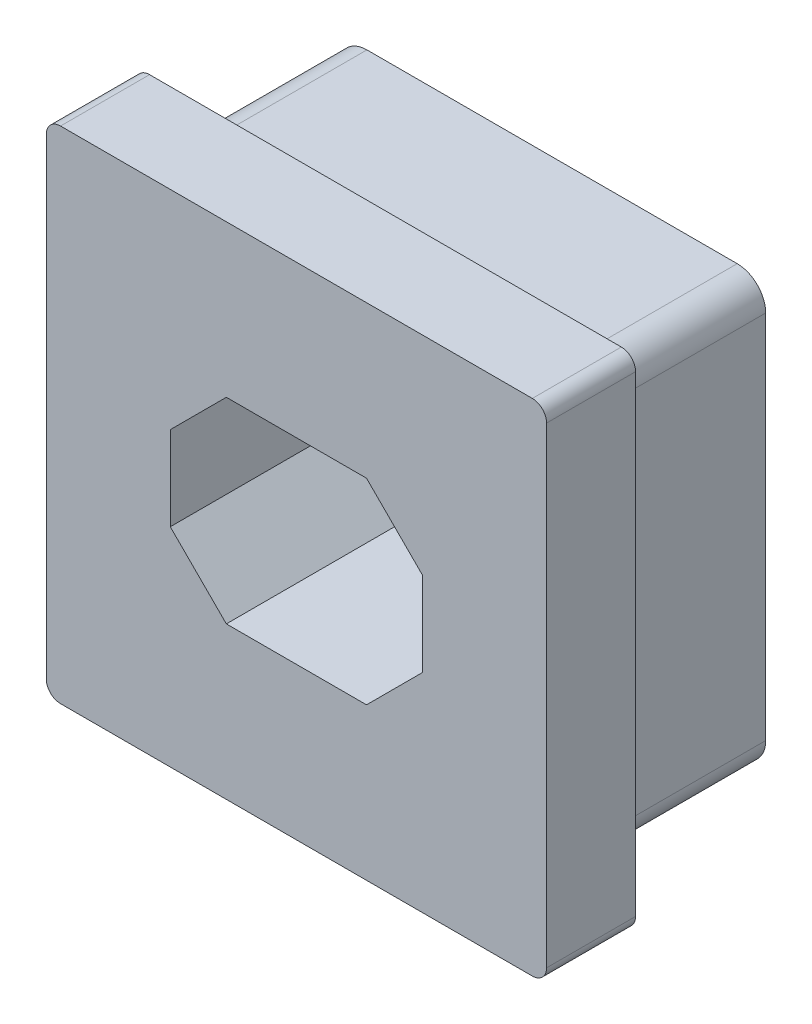
SolidWorks part; units mm, degrees
material "PET"
ref_plane "Front Plane" through (0, 0, 0) normal (0, 0, 1) x (1, 0, 0)
ref_plane "Top Plane" through (0, 0, 0) normal (0, 1, 0) x (1, 0, 0)
ref_plane "Right Plane" through (0, 0, 0) normal (1, 0, 0) x (0, 0, -1)
sketch "Sketch1" plane through (0, 0, 0) normal (0, 0, 1) x (1, 0, 0)
  line L0 (4.207, 4.715) -> (-4.207, 4.715) construction
  line L1 (4.715, -4.207) -> (4.715, 4.207) construction
  line L2 (-4.207, -4.715) -> (4.207, -4.715) construction
  line L3 (-4.715, 4.207) -> (-4.715, -4.207) construction
  line L4 (4.207, 4.715) -> (-4.207, 4.715) construction
  line L5 (4.715, -4.207) -> (4.715, 4.207) construction
  line L6 (-4.207, -4.715) -> (4.207, -4.715) construction
  line L7 (-4.715, 4.207) -> (-4.715, -4.207) construction
  line L8 (4.207, 4.461) -> (-4.207, 4.461)
  line L9 (-4.461, 4.207) -> (-4.461, -4.207)
  line L10 (-4.207, -4.461) -> (4.207, -4.461)
  line L11 (4.461, -4.207) -> (4.461, 4.207)
  arc A0 (4.715, 4.207) -> (4.207, 4.715) centre (4.207, 4.207) ccw construction
  arc A1 (4.207, -4.715) -> (4.715, -4.207) centre (4.207, -4.207) ccw construction
  arc A2 (-4.715, -4.207) -> (-4.207, -4.715) centre (-4.207, -4.207) ccw construction
  arc A3 (-4.207, 4.715) -> (-4.715, 4.207) centre (-4.207, 4.207) ccw construction
  arc A4 (4.715, 4.207) -> (4.207, 4.715) centre (4.207, 4.207) ccw construction
  arc A5 (4.207, -4.715) -> (4.715, -4.207) centre (4.207, -4.207) ccw construction
  arc A6 (-4.715, -4.207) -> (-4.207, -4.715) centre (-4.207, -4.207) ccw construction
  arc A7 (-4.207, 4.715) -> (-4.715, 4.207) centre (-4.207, 4.207) ccw construction
  arc A8 (-4.207, 4.461) -> (-4.461, 4.207) centre (-4.207, 4.207) ccw
  arc A9 (-4.461, -4.207) -> (-4.207, -4.461) centre (-4.207, -4.207) ccw
  arc A10 (4.207, -4.461) -> (4.461, -4.207) centre (4.207, -4.207) ccw
  arc A11 (4.461, 4.207) -> (4.207, 4.461) centre (4.207, 4.207) ccw
  dimension "D1" = 0.254
extrude "Boss-Extrude1" add sketch "Sketch1" along normal blind 1.5875
sketch "Sketch2" plane through (0, 0, 1.5875) normal (0, 0, 1) x (1, 0, 0)
  line L1 (-2.25, 1.75) -> (2.25, 1.75)
  line L2 (-2.25, 1.75) -> (-2.25, -1.75)
  line L3 (-2.25, -1.75) -> (2.25, -1.75)
  line L4 (2.25, 1.75) -> (2.25, -1.75)
  line L5 (-2.25, 1.75) -> (2.25, -1.75) construction
  line L6 (-2.25, -1.75) -> (2.25, 1.75) construction
  point P0 (0, 0)
  dimension "D1" = 4.5
  dimension "D2" = 3.5
extrude "Cut-Extrude1" cut sketch "Sketch2" against normal through all
chamfer "Chamfer1" distance 1 angle 45 4 edges at (-2.25, -1.75, 0.7937) (2.25, -1.75, 0.7937) (2.25, 1.75, 0.7937) (-2.25, 1.75, 0.7937)
sketch "Sketch3" plane through (0, 0, 0) normal (0, 0, -1) x (-1, 0, 0)
  line L2 (3.81, -3.81) -> (-3.81, -3.81)
  line L3 (3.81, -3.81) -> (3.81, 3.81)
  line L4 (3.81, 3.81) -> (-3.81, 3.81)
  line L5 (-3.81, -3.81) -> (-3.81, 3.81)
  line L6 (3.81, -3.81) -> (-3.81, 3.81) construction
  line L7 (3.81, 3.81) -> (-3.81, -3.81) construction
  line L9 (2.25, -0.75) -> (2.25, 0.75)
  line L10 (1.25, -1.75) -> (2.25, -0.75)
  line L11 (-1.25, -1.75) -> (1.25, -1.75)
  line L12 (-2.25, -0.75) -> (-1.25, -1.75)
  line L13 (-2.25, 0.75) -> (-2.25, -0.75)
  line L14 (-1.25, 1.75) -> (-2.25, 0.75)
  line L15 (1.25, 1.75) -> (-1.25, 1.75)
  line L16 (2.25, 0.75) -> (1.25, 1.75)
  line L17 (2.25, -0.75) -> (2.25, 0.75)
  line L18 (1.25, -1.75) -> (2.25, -0.75)
  line L19 (-1.25, -1.75) -> (1.25, -1.75)
  line L20 (-2.25, -0.75) -> (-1.25, -1.75)
  line L21 (-2.25, 0.75) -> (-2.25, -0.75)
  line L22 (-1.25, 1.75) -> (-2.25, 0.75)
  line L23 (1.25, 1.75) -> (-1.25, 1.75)
  line L24 (2.25, 0.75) -> (1.25, 1.75)
  point P2 (0, 0)
  point P12 (3.7879, 3.7522)
  dimension "D2" = 7.62
  dimension "D3" = 7.62
  dimension "D1" = 0
extrude "Boss-Extrude2" add sketch "Sketch3" along normal blind 2.9718
fillet "Fillet1" radius 0.508 4 edges at (3.81, 3.81, -1.4859) (-3.81, 3.81, -1.4859) (-3.81, -3.81, -1.4859) (3.81, -3.81, -1.4859)
